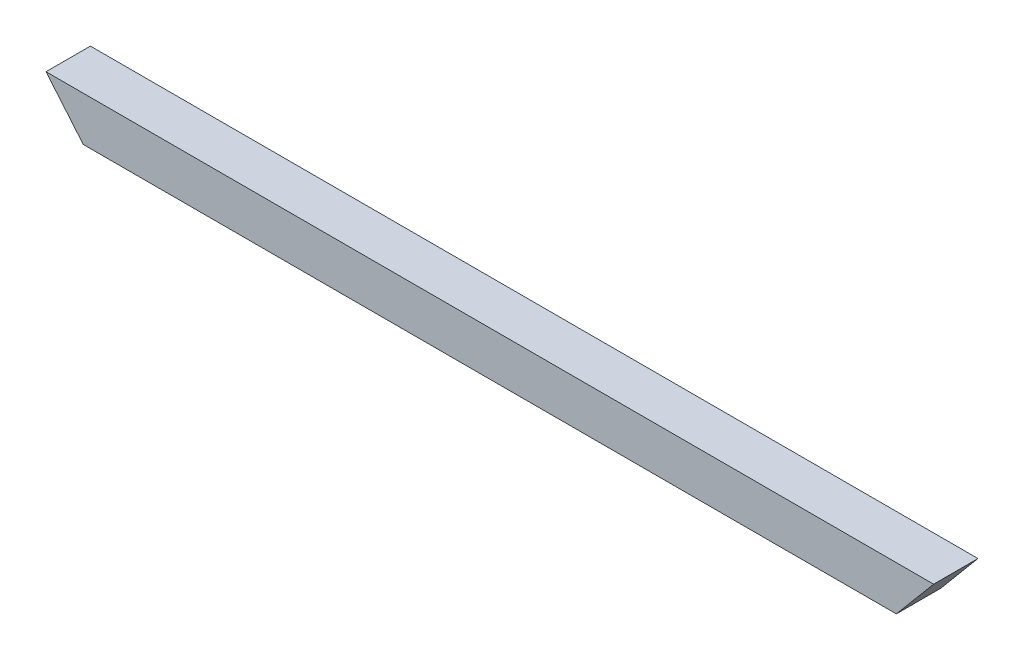
SolidWorks part; units mm, degrees
ref_plane "Front Plane" through (0, 0, 0) normal (0, 0, 1) x (1, 0, 0)
ref_plane "Top Plane" through (0, 0, 0) normal (0, 1, 0) x (1, 0, 0)
ref_plane "Right Plane" through (0, 0, 0) normal (1, 0, 0) x (0, 0, -1)
sketch "Sketch1" plane through (0, 0, 0) normal (0, 0, -1) x (1, 0, 0)
  line L0 (-31.9697, -38.1) -> (0, 0)
  line L1 (-31.9697, -38.1) -> (730.0303, -38.1)
  line L3 (0, 0) -> (698.0606, 0)
  line L5 (730.0303, -38.1) -> (698.0606, 0)
  dimension "D1" = 762
  dimension "D2" = 50
  dimension "D3" = 38.1
extrude "Boss-Extrude1" add sketch "Sketch1" along normal blind 38.1
